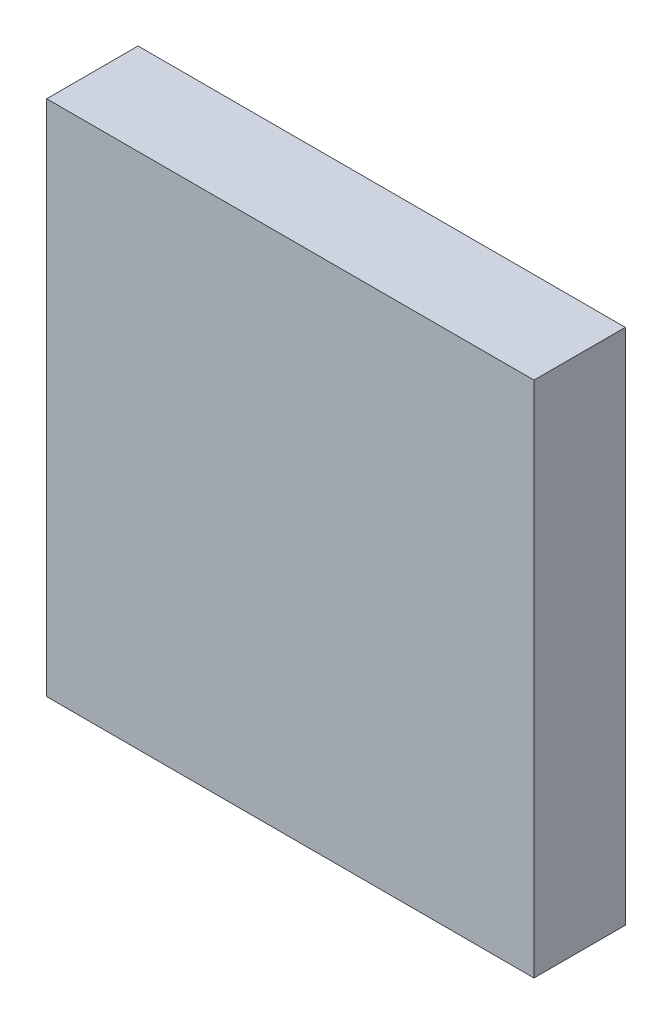
SolidWorks part; units mm, degrees
ref_plane "Front Plane" through (0, 0, 0) normal (0, 0, 1) x (1, 0, 0)
ref_plane "Top Plane" through (0, 0, 0) normal (0, 1, 0) x (1, 0, 0)
ref_plane "Right Plane" through (0, 0, 0) normal (1, 0, 0) x (0, 0, -1)
sketch "Sketch1" plane through (0, 0, 0) normal (0, 1, 0) x (1, 0, 0)
  line L1 (-50.8, -9.525) -> (50.8, -9.525)
  line L2 (-50.8, -9.525) -> (-50.8, 9.525)
  line L3 (-50.8, 9.525) -> (50.8, 9.525)
  line L4 (50.8, -9.525) -> (50.8, 9.525)
  line L5 (-50.8, -9.525) -> (50.8, 9.525) construction
  line L6 (-50.8, 9.525) -> (50.8, -9.525) construction
  point P0 (0, 0)
  dimension "D1" = 19.05
  dimension "D2" = 101.6
extrude "Boss-Extrude1" add sketch "Sketch1" along normal blind 107.95
